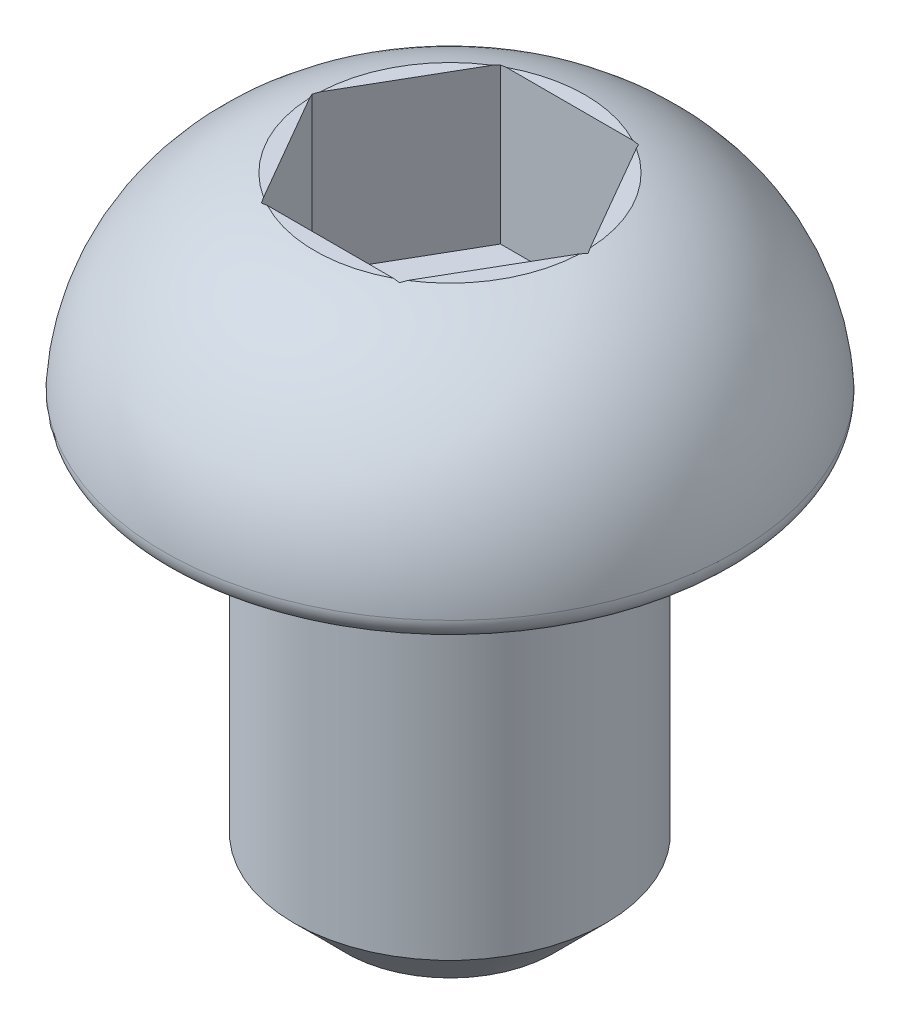
SolidWorks part; units mm, degrees
ref_plane "前视" through (0, 0, 0) normal (0, 0, 1) x (1, 0, 0)
ref_plane "上视" through (0, 0, 0) normal (0, 1, 0) x (1, 0, 0)
ref_plane "右视" through (0, 0, 0) normal (1, 0, 0) x (0, 0, -1)
sketch "草图1" plane through (0, 0, 0) normal (0, 0, 1) x (1, 0, 0)
  line L0 (0, 0) -> (0, 2)
  line L1 (0, 2) -> (1.3, 2)
  line L2 (0, 0) -> (2.75, 0)
  arc A0 (1.3, 2) -> (2.75, 0) centre (0.7515, 0.0767) cw
  dimension "D4" = 2
  dimension "D1" = 1.3
  dimension "D2" = 2.75
  dimension "D3" = 2
revolve "旋转1" add sketch "草图1" angle 360 about L0
fillet "圆角1" radius 0.2 1 edges at (0, 0, -2.75)
sketch "草图2" plane through (0, 2, 0) normal (0, 1, 0) x (1, 0, 0)
  line L1 (1.3279, 0) -> (0.664, 1.15)
  line L2 (0.664, 1.15) -> (-0.664, 1.15)
  line L3 (-0.664, 1.15) -> (-1.3279, 0)
  line L4 (-1.3279, 0) -> (-0.664, -1.15)
  line L5 (-0.664, -1.15) -> (0.664, -1.15)
  line L6 (0.664, -1.15) -> (1.3279, 0)
  circle A0 centre (0, 0) radius 1.15 construction
  dimension "D1" = 2.3
extrude "切除-拉伸1" cut sketch "草图2" against normal blind 1.5
sketch "草图3" plane through (0, 0, 0) normal (0, -1, 0) x (1, 0, 0)
  circle A0 centre (0, 0) radius 1.5
  dimension "D1" = 3
extrude "凸台-拉伸1" add sketch "草图3" along normal blind 4
chamfer "倒角1" distance 0.5 angle 45 1 edges at (0, -4, -1.5)
